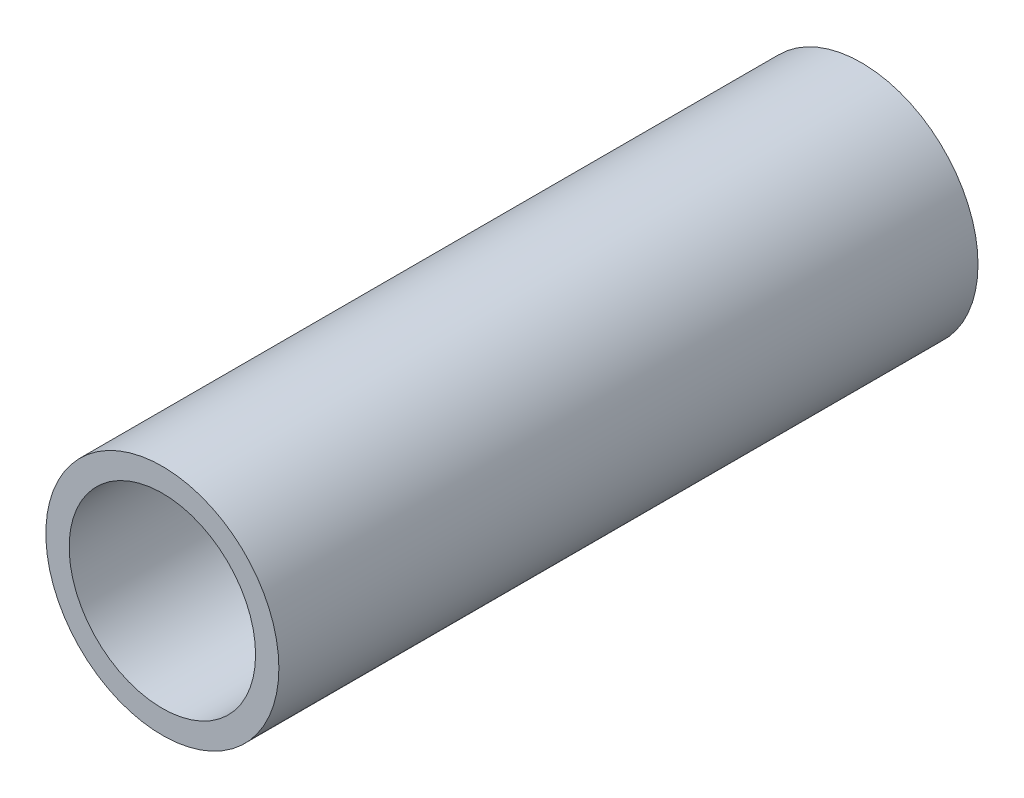
SolidWorks part; units mm, degrees
material "PVC Rigid"
ref_plane "Front Plane" through (0, 0, 0) normal (0, 0, 1) x (1, 0, 0)
ref_plane "Top Plane" through (0, 0, 0) normal (0, 1, 0) x (1, 0, 0)
ref_plane "Right Plane" through (0, 0, 0) normal (1, 0, 0) x (0, 0, -1)
sketch "Sketch1" plane through (0, 0, 0) normal (0, 0, 1) x (1, 0, 0)
  circle A0 centre (0, 0) radius 12.7
  circle A1 centre (0, 0) radius 10.16
  dimension "D1" = 25.4
  dimension "D2" = 20.32
extrude "Boss-Extrude1" add sketch "Sketch1" along normal blind 76.2
